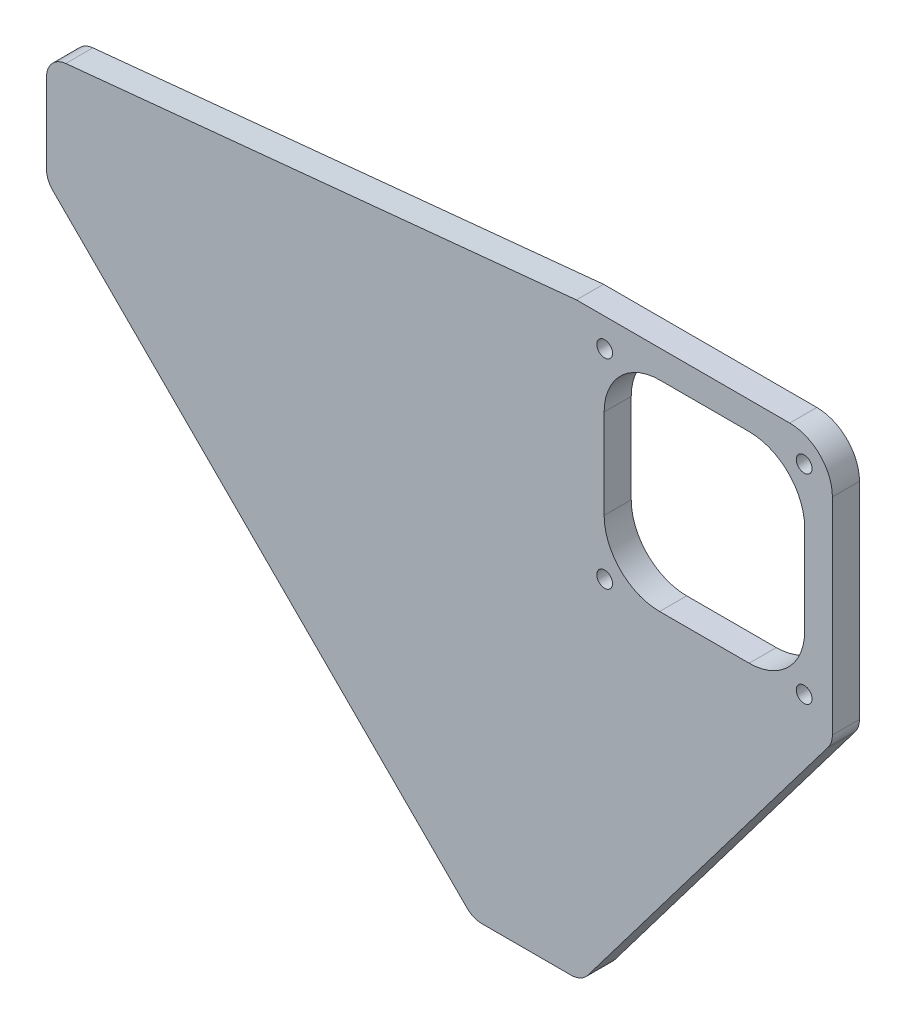
SolidWorks part; units mm, degrees
ref_plane "Front Plane" through (0, 0, 0) normal (0, 0, 1) x (1, 0, 0)
ref_plane "Top Plane" through (0, 0, 0) normal (0, 1, 0) x (1, 0, 0)
ref_plane "Right Plane" through (0, 0, 0) normal (1, 0, 0) x (0, 0, -1)
sketch "Sketch1" plane through (0, 0, 0) normal (0, 0, 1) x (1, 0, 0)
  line L0 (-100, 0) -> (0, -100)
  line L5 (0, -100) -> (25.4, -100)
  line L6 (25.4, -100) -> (25.4, 25.4)
  line L7 (25.4, 25.4) -> (-100, 25.4)
  line L8 (-100, 25.4) -> (-100, 0)
  line L9 (0, 0) -> (25.4, 25.4) construction
  line L10 (-25.4, 25.4) -> (25.4, -25.4)
  line L11 (24.2, 37.7) -> (-100, 25.4)
  line L12 (24.2, 37.7) -> (84.2, 37.7)
  line L13 (24.2, 37.7) -> (24.2, -22.3)
  line L14 (24.2, -22.3) -> (84.2, -22.3)
  line L15 (84.2, 37.7) -> (84.2, -22.3)
  line L16 (24.2, 37.7) -> (84.2, -22.3) construction
  line L17 (24.2, -22.3) -> (84.2, 37.7) construction
  line L18 (84.2, -22.3) -> (25.4, -100)
  point P11 (0, 0)
  point P15 (0, 0)
  dimension "D1" = 125.4
  dimension "D2" = 125.4
  dimension "D3" = 25.4
  dimension "D4" = 25.4
  dimension "D5" = 71.842
  dimension "D6" = 35.921
  dimension "D7" = 60
  dimension "D8" = 60
  dimension "D9" = 1.2
  dimension "D10" = 12.3
extrude "Boss-Extrude1" add sketch "Sketch1" along normal blind 6.35 contours L7 L8 L0 L5 L6
sketch "Sketch2" plane through (0, 0, 0) normal (0, 0, 1) x (1, 0, 0)
  line L1 (24.2, 37.7) -> (84.2, 37.7)
  line L4 (84.2, 37.7) -> (84.2, -22.3)
  line L5 (24.2, 37.7) -> (84.2, -22.3) construction
  line L6 (24.2, -22.3) -> (84.2, 37.7) construction
  line L7 (25.4, 25.4) -> (-100, 25.4) construction
  line L8 (24.2, 37.7) -> (-100, 25.4)
  line L9 (84.2, -22.3) -> (25.4, -100)
  line L10 (25.4, -100) -> (24.2, -22.3)
  line L11 (-100, 25.4) -> (24.2, -22.3)
  point P0 (54.2, 7.7)
  dimension "D1" = 60
  dimension "D2" = 60
  dimension "D4" = 12.3
extrude "Boss-Extrude2" add sketch "Sketch2" along normal blind 6.35
fillet "Fillet1" radius 10 1 edges at (84.2, 37.7, 3.175)
fillet "Fillet2" radius 5 5 edges at (-100, 25.4, 3.175) (-100, 0, 3.175) (0, -100, 3.175) (25.4, -100, 3.175) (84.2, -22.3, 3.175)
sketch "Sketch3" plane through (0, 0, 6.35) normal (0, 0, 1) x (1, 0, 0)
  line L0 (74.2, 37.7) -> (24.2, 37.7) construction
  line L1 (43.7, 31.2) -> (64.7, 31.2)
  line L2 (30.7, 18.2) -> (30.7, -2.8)
  line L3 (43.7, -15.8) -> (64.7, -15.8)
  line L4 (77.7, 18.2) -> (77.7, -2.8)
  line L5 (30.7, 31.2) -> (77.7, -15.8) construction
  line L6 (30.7, -15.8) -> (77.7, 31.2) construction
  line L7 (84.2, -20.6214) -> (84.2, 27.7) construction
  arc A0 (30.7, -2.8) -> (43.7, -15.8) centre (43.7, -2.8) ccw
  arc A1 (64.7, -15.8) -> (77.7, -2.8) centre (64.7, -2.8) ccw
  arc A2 (64.7, 31.2) -> (77.7, 18.2) centre (64.7, 18.2) cw
  arc A3 (43.7, 31.2) -> (30.7, 18.2) centre (43.7, 18.2) ccw
  point P0 (54.2, 7.7)
  dimension "D5" = 13
  dimension "D1" = 47
  dimension "D2" = 47
  dimension "D3" = 6.5
  dimension "D4" = 6.5
extrude "Cut-Extrude1" cut sketch "Sketch3" against normal through all
sketch "Sketch4" plane through (0, 0, 0) normal (0, 0, -1) x (-1, 0, 0)
  line L0 (-81.2711, 34.7711) -> (-73.8924, 27.3924) construction
  line L2 (-77.5817, 31.0817) -> (-30.8217, 31.0817)
  line L3 (-77.5817, 31.0817) -> (-77.5817, -15.6783)
  line L4 (-77.5817, -15.6783) -> (-30.8217, -15.6783)
  line L5 (-30.8217, 31.0817) -> (-30.8217, -15.6783)
  arc A0 (-74.2, 37.7) -> (-84.2, 27.7) centre (-74.2, 27.7) ccw construction
  arc A1 (-64.7, 31.2) -> (-77.7, 18.2) centre (-64.7, 18.2) ccw construction
  circle A2 centre (-77.5817, 31.0817) radius 1.85
  circle A3 centre (-30.8217, 31.0817) radius 1.85
  circle A4 centre (-30.8217, -15.6783) radius 1.85
  circle A5 centre (-77.5817, -15.6783) radius 1.85
  dimension "D1" = 3.7
  dimension "D4" = 3.7
  dimension "D5" = 3.7
  dimension "D6" = 3.7
  dimension "D2" = 46.76
  dimension "D3" = 46.76
extrude "Cut-Extrude2" cut sketch "Sketch4" against normal through all contours A4 | A3 | A2 | A5
